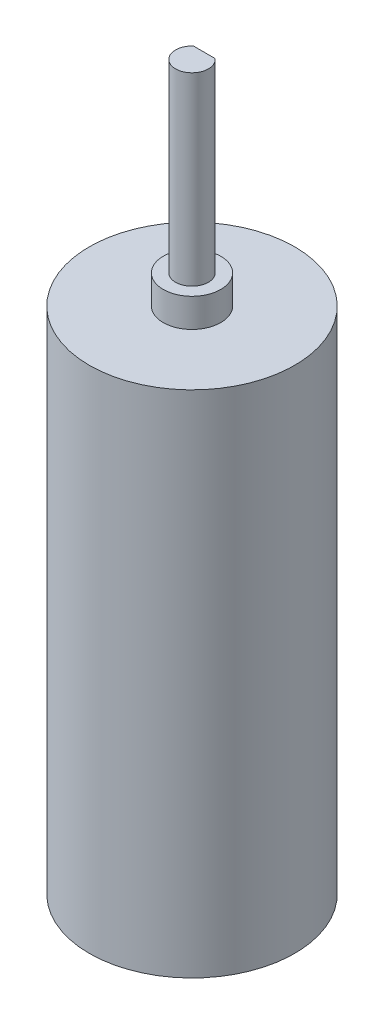
SolidWorks part; units mm, degrees
ref_plane "前视基准面" through (0, 0, 0) normal (0, 0, 1) x (1, 0, 0)
ref_plane "上视基准面" through (0, 0, 0) normal (0, 1, 0) x (1, 0, 0)
ref_plane "右视基准面" through (0, 0, 0) normal (1, 0, 0) x (0, 0, -1)
sketch "草图1" plane through (0, 0, 0) normal (0, 1, 0) x (1, 0, 0)
  circle A0 centre (0, 0) radius 12.5
  dimension "D1" = 25
extrude "凸台-拉伸1" add sketch "草图1" along normal blind 62
sketch "草图2" plane through (0, 62, 0) normal (0, 1, 0) x (1, 0, 0)
  circle A0 centre (0, 0) radius 3.5
  dimension "D1" = 7
extrude "凸台-拉伸2" add sketch "草图2" along normal blind 3.5
sketch "草图3" plane through (0, 65.5, 0) normal (0, 1, 0) x (1, 0, 0)
  circle A0 centre (0, 0) radius 2
  dimension "D1" = 4
extrude "凸台-拉伸3" add sketch "草图3" along normal blind 22.5
sketch "草图4" plane through (0, 88, 0) normal (0, 1, 0) x (1, 0, 0)
  line L0 (-1.3229, 1.5) -> (1.3229, 1.5)
  circle A0 centre (0, 0) radius 2 construction
  circle A1 centre (0, 0) radius 2
  circle M2 centre (0, 0) radius 2
  dimension "D1" = 1.5
extrude "切除-拉伸1" cut sketch "草图4" against normal blind 18.5 contours L0 M2
